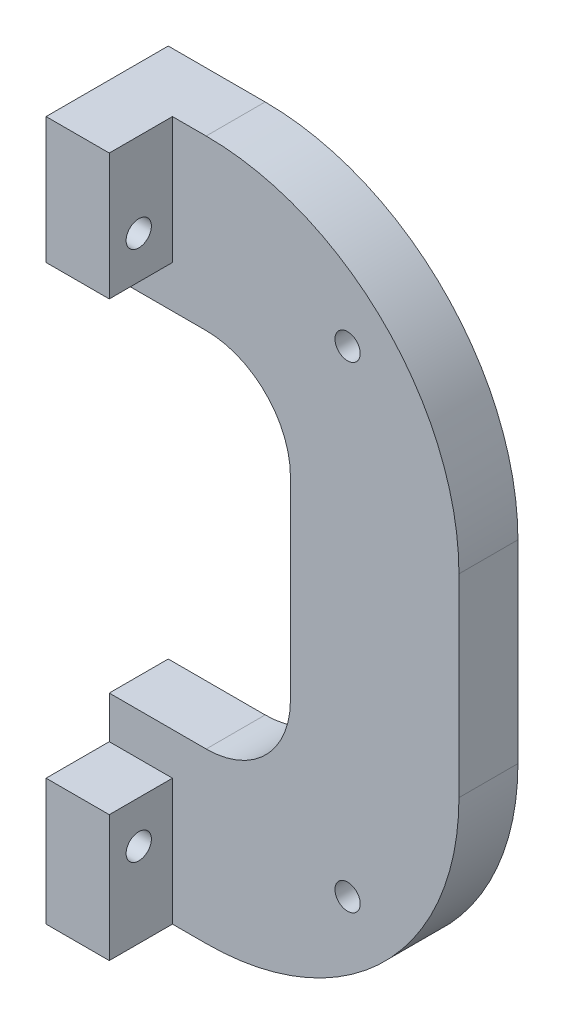
SolidWorks part; units mm, degrees
ref_plane "Front Plane" through (0, 0, 0) normal (0, 0, 1) x (1, 0, 0)
ref_plane "Top Plane" through (0, 0, 0) normal (0, 1, 0) x (1, 0, 0)
ref_plane "Right Plane" through (0, 0, 0) normal (1, 0, 0) x (0, 0, -1)
sketch "Sketch1" plane through (0, 0, 0) normal (0, 0, 1) x (1, 0, 0)
  line L4 (0, 21.5) -> (0, -21.5)
  line L5 (0, -21.5) -> (11.5, -21.5)
  line L6 (21.5, -11.5) -> (21.5, 11.5)
  line L7 (11.5, 21.5) -> (0, 21.5)
  line L8 (11.5, 41.5) -> (0, 41.5)
  line L10 (0, -41.5) -> (11.5, -41.5)
  line L11 (41.5, -11.5) -> (41.5, 11.5)
  line L12 (0, 21.5) -> (0, 41.5)
  line L13 (0, -21.5) -> (0, -41.5)
  line L15 (-20, -41.5) -> (11.5, -41.5) construction
  line L16 (-20, 41.5) -> (-20, -41.5) construction
  line L17 (11.5, 41.5) -> (-20, 41.5) construction
  arc A4 (11.5, -21.5) -> (21.5, -11.5) centre (11.5, -11.5) ccw
  arc A5 (21.5, 11.5) -> (11.5, 21.5) centre (11.5, 11.5) ccw
  arc A6 (11.5, -41.5) -> (41.5, -11.5) centre (11.5, -11.5) ccw
  arc A7 (41.5, 11.5) -> (11.5, 41.5) centre (11.5, 11.5) ccw
  dimension "D5" = 20
  dimension "D4" = 10
  dimension "D1" = 21.5
  dimension "D2" = 43
  dimension "D3" = 21.5
extrude "Boss-Extrude4" add sketch "Sketch1" along normal blind 7 contours L11 A7 L8 L12 L7 A5 L6 A4 L5 L13 L10 A6
sketch "Sketch6" plane through (0, 0, 7) normal (0, 0, 1) x (1, 0, 0)
  line L0 (0, 21.5) -> (0, 41.5)
  line L1 (0, 41.5) -> (7.5, 41.5)
  line L2 (11.5, 41.5) -> (0, 41.5) construction
  line L3 (7.5, 41.5) -> (7.5, 21.5)
  line L4 (11.5, 21.5) -> (0, 21.5) construction
  line L5 (7.5, 21.5) -> (0, 21.5)
  line L6 (0, 0) -> (11.6332, 0) construction
  line L7 (7.5, -41.5) -> (7.5, -21.5)
  line L8 (0, -41.5) -> (7.5, -41.5)
  line L9 (0, -21.5) -> (0, -41.5)
  line L10 (7.5, -21.5) -> (0, -21.5)
  dimension "D1" = 7.5
extrude "Boss-Extrude5" add sketch "Sketch6" along normal blind 7.5
sketch "Sketch7" plane through (7.5, 0, 0) normal (1, 0, 0) x (0, 0, -1)
  line L0 (-14.5, 21.5) -> (-14.5, 41.5) construction
  line L1 (-14.5, 41.5) -> (-7, 41.5) construction
  line L2 (0, 0) -> (-19.6903, 0) construction
  circle A0 centre (-11, 31.5) radius 1.5
  circle A1 centre (-11, -31.5) radius 1.5
  dimension "D1" = 3
  dimension "D2" = 3.5
  dimension "D3" = 10
extrude "Cut-Extrude3" cut sketch "Sketch7" against normal blind 7.5
sketch "Sketch8" plane through (0, 0, 7) normal (0, 0, 1) x (1, 0, 0)
  line L0 (0, 0) -> (54.4133, 0) construction
  line L1 (0, 0) -> (47.8523, 47.8523) construction
  line L2 (0, 0) -> (47.8523, -47.8523) construction
  circle A0 centre (28.2843, 28.2843) radius 1.5
  circle A1 centre (28.2843, -28.2843) radius 1.5
  dimension "D2" = 3
  dimension "D3" = 3
  dimension "D1" = 45
  dimension "D4" = 40
  dimension "D5" = 40
extrude "Cut-Extrude4" cut sketch "Sketch8" against normal blind 7.5
sketch "Sketch9" plane through (7.5, 0, 0) normal (1, 0, 0) x (0, 0, -1)
  line L0 (-7, 21.5) -> (-14.5, 21.5)
  line L1 (-14.5, 21.5) -> (-14.5, 26.5)
  line L2 (-14.5, 21.5) -> (-14.5, 41.5) construction
  line L3 (-14.5, 26.5) -> (-7, 26.5)
  line L4 (-7, 21.5) -> (-7, 41.5) construction
  line L5 (-7, 26.5) -> (-7, 21.5)
  line L6 (0, 0) -> (14.7936, 0) construction
  line L7 (-14.5, -26.5) -> (-7, -26.5)
  line L8 (-14.5, -21.5) -> (-14.5, -26.5)
  line L9 (-7, -21.5) -> (-14.5, -21.5)
  line L10 (-7, -26.5) -> (-7, -21.5)
  dimension "D1" = 5
extrude "Cut-Extrude5" cut sketch "Sketch9" against normal blind 7.5
